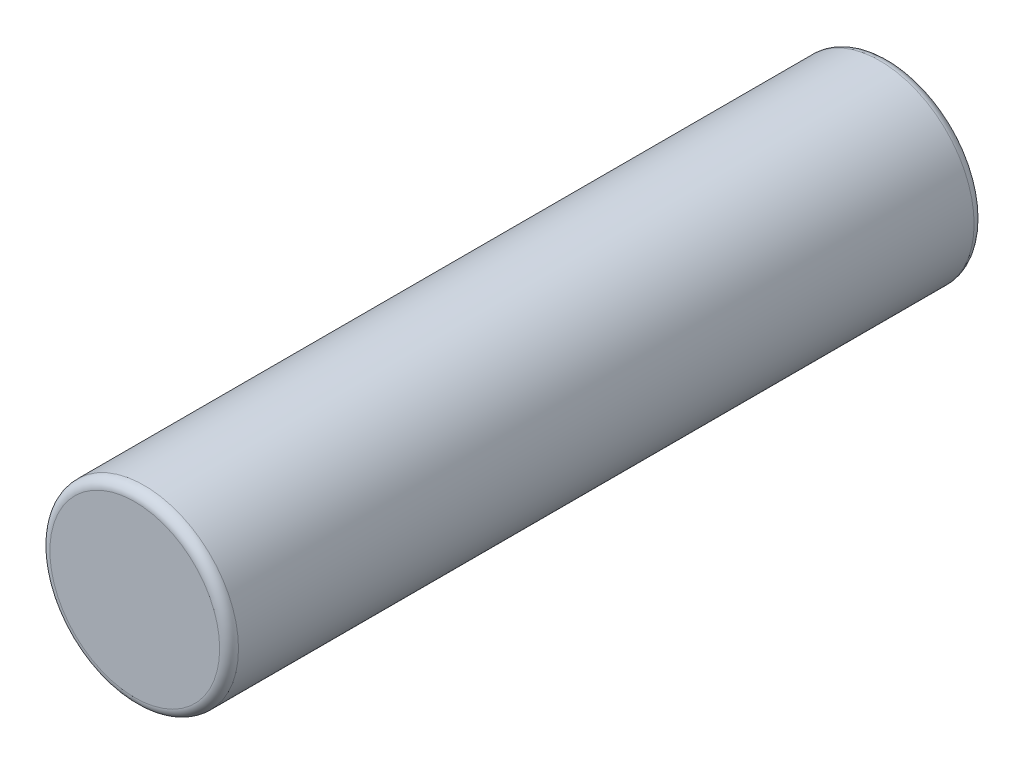
SolidWorks part; units mm, degrees
material "Stainless Steel (ferritic)"
ref_plane "Front Plane" through (0, 0, 0) normal (0, 0, 1) x (1, 0, 0)
ref_plane "Top Plane" through (0, 0, 0) normal (0, 1, 0) x (1, 0, 0)
ref_plane "Right Plane" through (0, 0, 0) normal (1, 0, 0) x (0, 0, -1)
sketch "Sketch2" plane through (0, 0, 0) normal (0, 0, 1) x (1, 0, 0)
  circle A0 centre (0, 0) radius 1
  dimension "D1" = 2
extrude "Boss-Extrude1" add sketch "Sketch2" along normal blind 8
fillet "Fillet1" radius 0.1 2 edges at (1, 0, 0) (1, 0, 8)
